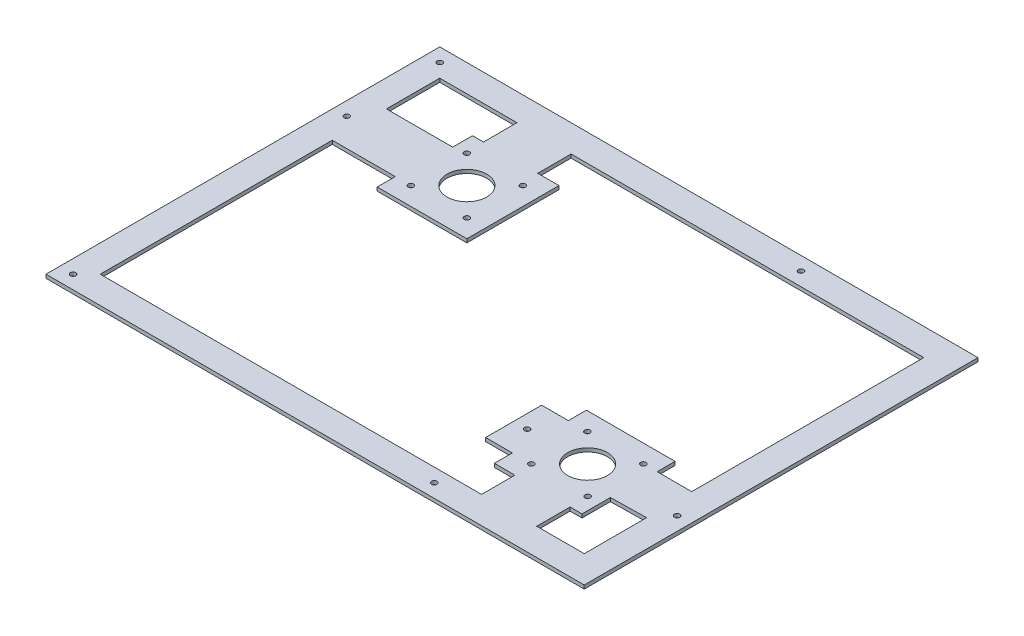
SolidWorks part; units mm, degrees
ref_plane "Front Plane" through (0, 0, 0) normal (0, 0, 1) x (1, 0, 0)
ref_plane "Top Plane" through (0, 0, 0) normal (0, 1, 0) x (1, 0, 0)
ref_plane "Right Plane" through (0, 0, 0) normal (1, 0, 0) x (0, 0, -1)
sketch "Sketch1" plane through (0, 0, 0) normal (1, 0, 0) x (0, 0, -1)
  line L0 (-26.6783, 0) -> (191.3217, 0)
  line L1 (119.9, 0) -> (-119.9, 0) construction
  line L2 (-26.6783, 0) -> (-26.6783, 2)
  line L3 (191.3217, 0) -> (191.3217, 2)
  line L4 (191.3217, 2) -> (-26.6783, 2)
  dimension "D1" = 218
  dimension "D2" = 2
extrude "Boss-Extrude1" add sketch "Sketch1" along normal blind 298 contours L4 L2 L0 L3
sketch "Sketch2" plane through (0, 2, 0) normal (0, 1, 0) x (1, 0, 0)
  line L0 (0, -1.1) -> (0, 1.1) construction
  line L5 (298, 191.3217) -> (0, 191.3217) construction
  line L6 (15, 176.3217) -> (57.7212, 176.3217)
  line L7 (128.5445, 82.3217) -> (183.6204, 82.3217) construction
  line L18 (74, 132.3217) -> (85, 132.3217) construction
  line L20 (149, 244.2227) -> (149, 176.3217) construction
  line L23 (15, 176.3217) -> (15, 159.517)
  line L24 (298, -26.6783) -> (0, -26.6783) construction
  line L27 (85, 132.3217) -> (-63.8787, 132.3217) construction
  line L28 (149, -11.6783) -> (104.4712, -11.6783)
  line L29 (99.5, 106.8217) -> (99.5, 157.8217)
  line L30 (101.2006, 176.3217) -> (149, 176.3217)
  line L31 (51.6521, 157.8217) -> (57.7212, 157.8217)
  line L32 (104.4712, -11.6783) -> (15, -11.6783)
  line L34 (99.5, 106.8217) -> (49.8733, 106.8217)
  line L35 (15, -11.6783) -> (15, 89.9418)
  line L36 (57.7212, 176.3217) -> (57.7212, 157.8217)
  line L37 (99.5, 157.8217) -> (87.7212, 157.8217)
  line L39 (101.2006, 176.3217) -> (87.7212, 176.3217)
  line L40 (87.7212, 157.8217) -> (87.7212, 176.3217)
  line L42 (15, 89.9418) -> (15, 116.8217)
  line L43 (15, 116.8217) -> (49.8733, 116.8217)
  line L44 (49.8733, 106.8217) -> (49.8733, 116.8217)
  line L46 (15, 159.517) -> (15, 146.8217)
  line L47 (15, 146.8217) -> (51.6521, 146.8217)
  line L48 (51.6521, 157.8217) -> (51.6521, 146.8217)
  line L49 (283, 47.8217) -> (283, 176.3217)
  line L50 (283, 176.3217) -> (149, 176.3217)
  line L51 (226.1545, -11.6783) -> (149, -11.6783)
  line L52 (149, -11.6783) -> (149, -99.356) construction
  line L62 (214.9875, 235.2083) -> (214.9875, 57.7194) construction
  line L63 (283, 47.8217) -> (263.8762, 47.8217)
  line L64 (283, -11.6783) -> (283, 10.1264)
  line L65 (283, 10.1264) -> (283, 22.8217)
  line L66 (283, 22.8217) -> (263.3054, 22.4886)
  line L67 (263.3054, 6.7817) -> (263.3054, 22.4886)
  line L68 (263.3054, 6.7817) -> (256.6954, 6.7817)
  line L69 (256.6954, -11.6783) -> (256.6954, 6.7817)
  line L70 (283, -11.6783) -> (256.6954, -11.6783)
  line L71 (214.7904, 57.7194) -> (214.7904, 47.7194)
  line L72 (214.7904, 57.7194) -> (263.8762, 57.7194)
  line L73 (214.7904, 6.7771) -> (226.1545, 6.7771)
  line L75 (226.1545, 6.7771) -> (226.1545, -11.6783)
  line L76 (263.8762, 57.7194) -> (263.8762, 47.8217)
  line L77 (214.7904, 16.7194) -> (214.7904, 6.7771)
  line L78 (214.7904, 47.7194) -> (199.9904, 47.7194)
  line L80 (214.7904, 16.7194) -> (199.9904, 16.7194)
  line L81 (199.9904, 47.7194) -> (199.9904, 16.7194)
  line L82 (214.9875, 6.7771) -> (214.9875, -106.0424) construction
  line L83 (298, 191.3217) -> (298, -26.6783) construction
  circle A0 centre (74, 132.3217) radius 11
  circle A4 centre (89.5, 116.8217) radius 1.5
  circle A5 centre (58.5, 116.8217) radius 1.5
  circle A6 centre (89.5, 147.8217) radius 1.5
  circle A7 centre (58.5, 147.8217) radius 1.5
  circle A13 centre (256.3313, 47.7194) radius 1.5
  circle A14 centre (256.4575, 16.7194) radius 1.5
  circle A15 centre (225.3313, 16.7194) radius 1.5
  circle A16 centre (225.3313, 47.7194) radius 1.5
  circle A17 centre (240.9575, 32.2194) radius 11
  circle A18 centre (290.5, 32.2194) radius 1.5
  circle A19 centre (7.5, 132.3217) radius 1.5
  circle A20 centre (207.4904, 32.2194) radius 1.5
  circle A21 centre (207.4904, 183.8217) radius 1.5
  circle A22 centre (207.4904, -19.1783) radius 1.5
  circle A23 centre (7.5, -19.1783) radius 1.5
  circle A24 centre (7.5, 183.8217) radius 1.5
  point P52 (57.7212, 167.0717)
  dimension "D9" = 22
  dimension "D10" = 3
  dimension "D11" = 3
  dimension "D31" = 3
  dimension "D32" = 3
  dimension "D37" = 3
  dimension "D38" = 3
  dimension "D40" = 3
  dimension "D42" = 3
  dimension "D44" = 3
  dimension "D45" = 7.5
  dimension "D2" = 50
  dimension "D3" = 150
  dimension "D4" = 109
  dimension "D5" = 15
  dimension "D6" = 15
  dimension "D7" = 30
  dimension "D8" = 31
  dimension "D12" = 31
  dimension "D13" = 15.5
  dimension "D14" = 15.5
  dimension "D15" = 149
  dimension "D16" = 30
  dimension "D17" = 15
  dimension "D18" = 15
  dimension "D19" = 10
  dimension "D20" = 10
  dimension "D21" = 10
  dimension "D22" = 10
  dimension "D23" = 10
  dimension "D24" = 15
  dimension "D25" = 7.5
  dimension "D26" = 15
  dimension "D27" = 15
  dimension "D28" = 18.46
  dimension "D29" = 34.6946
  dimension "D30" = 15
  dimension "D33" = 7.5
  dimension "D34" = 68.2096
  dimension "D35" = 14.8
  dimension "D36" = 7.5
  dimension "D39" = 7.5
  dimension "D41" = 7.5
  dimension "D43" = 7.5
extrude "Cut-Extrude1" cut sketch "Sketch2" against normal blind 10
